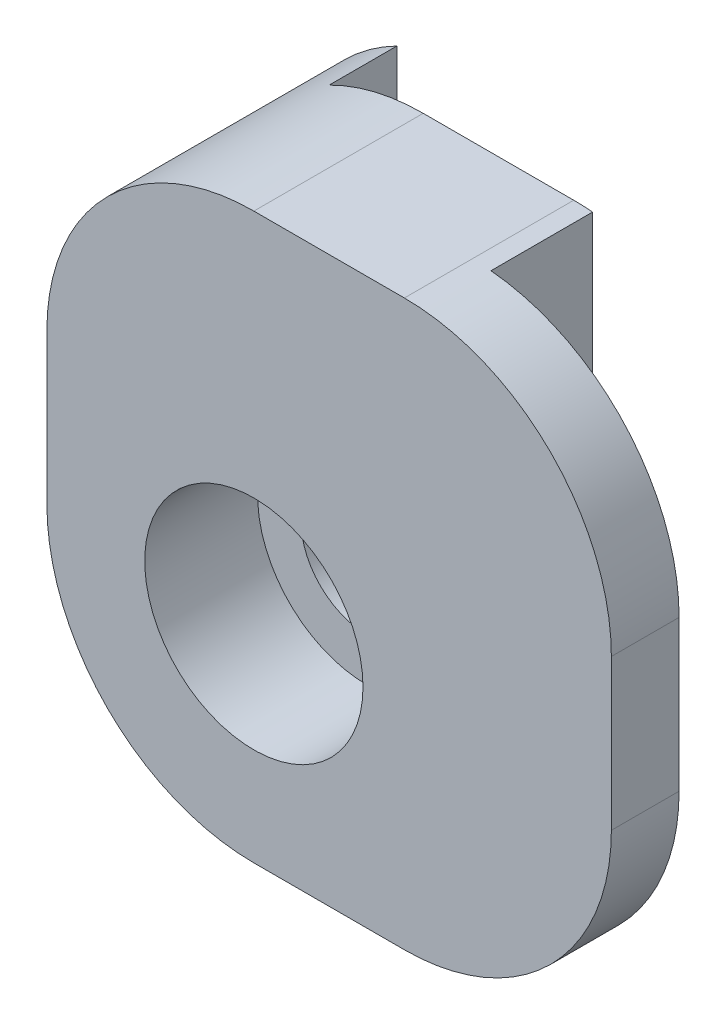
SolidWorks part; units mm, degrees
ref_plane "Plano frontal" through (0, 0, 0) normal (0, 0, 1) x (1, 0, 0)
ref_plane "Plano superior" through (0, 0, 0) normal (0, 1, 0) x (1, 0, 0)
ref_plane "Plano direito" through (0, 0, 0) normal (1, 0, 0) x (0, 0, -1)
sketch "Esboço3" plane through (0, 0, 0) normal (0, 0, 1) x (1, 0, 0)
  line L0 (0, 0) -> (-2.5, 2.5) construction
  line L1 (0, 0) -> (-7, 0)
  line L2 (0, 0) -> (0, 12)
  line L3 (0, 12) -> (-7, 12)
  line L4 (-7, 0) -> (-7, 12)
  circle A0 centre (-2.5, 2.5) radius 1.75
  dimension "D5" = 3.5
  dimension "D1" = 12
  dimension "D2" = 7
  dimension "D3" = 2.5
  dimension "D4" = 2.5
extrude "Ressalto-extrusão2" add sketch "Esboço3" along normal blind 2.7
sketch "Esboço4" plane through (0, 0, 2.7) normal (0, 0, 1) x (1, 0, 0)
  line L4 (0, 0) -> (0, 12)
  line L5 (0, 12) -> (-7, 12)
  line L6 (-7, 12) -> (-7, 0)
  line L7 (-7, 0) -> (0, 0)
  line L8 (0, 0) -> (0, 12)
  line L9 (0, 12) -> (-7, 12)
  line L10 (-7, 12) -> (-7, 0)
  line L11 (-7, 0) -> (0, 0)
  circle A0 centre (-2.5, 2.5) radius 1.75 construction
  circle A1 centre (-2.5, 2.5) radius 1.75
  dimension "D1" = 0
extrude "Ressalto-extrusão3" add sketch "Esboço4" along normal blind 2.1
sketch "Esboço5" plane through (-7, 0, 0) normal (-1, 0, 0) x (0, 0, 1)
  line L0 (4.8, 12) -> (4.8, 0) construction
  line L1 (4.8, 12) -> (4.8, 0)
  line L2 (2.7, 12) -> (2.7, 0)
  line L3 (4.8, 12) -> (2.7, 12)
  line L4 (2.7, 0) -> (4.8, 0)
  dimension "D1" = 2.1
extrude "Ressalto-extrusão4" add sketch "Esboço5" along normal blind 5
sketch "Esboço6" plane through (0, 0, 0) normal (0, -1, 0) x (1, 0, 0)
  line L6 (-7, 0) -> (0, 0)
  line L7 (0, 0) -> (0, 4.8)
  line L8 (0, 4.8) -> (-12, 4.8)
  line L9 (-12, 4.8) -> (-12, 2.7)
  line L10 (-12, 2.7) -> (-7, 2.7)
  line L11 (-7, 2.7) -> (-7, 0)
  line L12 (-7, 0) -> (0, 0)
  line L13 (0, 0) -> (0, 4.8)
  line L14 (0, 4.8) -> (-12, 4.8)
  line L15 (-12, 4.8) -> (-12, 2.7)
  line L16 (-12, 2.7) -> (-7, 2.7)
  line L17 (-7, 2.7) -> (-7, 0)
  dimension "D1" = 0
extrude "Ressalto-extrusão5" add sketch "Esboço6" along normal blind 3
sketch "Esboço7" plane through (0, 0, 0) normal (1, 0, 0) x (0, 0, -1)
  line L4 (0, -3) -> (0, 12)
  line L5 (0, 12) -> (-4.8, 12)
  line L6 (-4.8, 12) -> (-4.8, -3)
  line L7 (-4.8, -3) -> (0, -3)
  line L8 (0, -3) -> (0, 12)
  line L9 (0, 12) -> (-4.8, 12)
  line L10 (-4.8, 12) -> (-4.8, -3)
  line L11 (-4.8, -3) -> (0, -3)
  dimension "D1" = 0
extrude "Ressalto-extrusão6" add sketch "Esboço7" along normal blind 3
sketch "Esboço8" plane through (0, 0, 4.8) normal (0, 0, 1) x (1, 0, 0)
  circle A0 centre (-2.5, 2.5) radius 2.9
  dimension "D1" = 5.8
extrude "Corte-extrusão1" cut sketch "Esboço8" against normal blind 3
fillet "Filete1" radius 5.5 1 edges at (3, -3, 2.4)
sketch "Esboço10" plane through (0, 0, 0) normal (0, 0, -1) x (-1, 0, 0)
  line L0 (2.5, 2.5) -> (0, 0) construction
  line L1 (7, 12) -> (7, -3) construction
  line L2 (0, 0) -> (7, 0)
  line L3 (0, 0) -> (0, 14)
  line L4 (0, 14) -> (7, 14)
  line L5 (7, 0) -> (7, 14)
  line L6 (7, 12) -> (7, -3) construction
  line L7 (7, -3) -> (2.5, -3) construction
  line L8 (-3, 2.5) -> (-3, 12) construction
  line L9 (-3, 12) -> (7, 12) construction
  line L10 (7, -3) -> (2.5, -3)
  line L11 (-3, 2.5) -> (-3, 12)
  line L12 (-3, 12) -> (7, 12)
  line L13 (7, 12) -> (7, -3)
  arc A0 (-3, 2.5) -> (2.5, -3) centre (2.5, 2.5) ccw construction
  arc A1 (-3, 2.5) -> (2.5, -3) centre (2.5, 2.5) ccw
  line M10 (-3, 12) -> (-3, 2.5)
  arc M11 (-3, 2.5) -> (2.5, -3) centre (2.5, 2.5) ccw
  line M12 (2.5, -3) -> (7, -3)
  line M13 (7, -3) -> (7, 12)
  line M14 (7, 12) -> (-3, 12)
  dimension "D1" = 2.5
  dimension "D2" = 2.5
extrude "Ressalto-extrusão7" add sketch "Esboço10" along normal blind 1.5 contours L2 L3 M14 M10 M11 M12 M13
sketch "Esboço13" plane through (0, 0, 4.8) normal (0, 0, 1) x (1, 0, 0)
  line L0 (-2.5, -3) -> (-12, -3) construction
  line L1 (-12, -3) -> (-12, 12) construction
  line L6 (-12, -3) -> (-2.5, -3)
  line L7 (3, 2.5) -> (3, 12)
  line L8 (3, 12) -> (-12, 12)
  line L9 (-12, 12) -> (-12, -3)
  line L10 (-12, -3) -> (-6.5, -3)
  line L13 (-12, 2.5) -> (-12, -3)
  arc A0 (-12, 2.5) -> (-6.5, -3) centre (-6.5, 2.5) ccw
  arc A2 (-2.5, -3) -> (3, 2.5) centre (-2.5, 2.5) ccw
  dimension "D1" = 11
  dimension "D2" = 0
sketch "Esboço14" plane through (0, 0, 4.8) normal (0, 0, 1) x (1, 0, 0)
  line L4 (-12, -3) -> (-2.5, -3)
  line L5 (3, 2.5) -> (3, 12)
  line L6 (3, 12) -> (-12, 12)
  line L7 (-12, 12) -> (-12, -3)
  line L8 (-12, -3) -> (-2.5, -3)
  line L9 (3, 2.5) -> (3, 6.5)
  line L10 (-2.5, 12) -> (-6.5, 12)
  line L11 (-12, 6.5) -> (-12, -3)
  line L16 (3, 12) -> (3, 2.5) construction
  line L17 (-12, -3) -> (-12, 12) construction
  line L18 (3, 12) -> (-12, 12) construction
  line L19 (3, 12) -> (3, 2.5)
  line L20 (-12, -3) -> (-12, 12)
  line L21 (3, 12) -> (-12, 12)
  arc A0 (-12, 6.5) -> (-6.5, 12) centre (-6.5, 6.5) cw
  arc A1 (-2.5, 12) -> (3, 6.5) centre (-2.5, 6.5) cw
  arc A3 (-2.5, -3) -> (3, 2.5) centre (-2.5, 2.5) ccw
  arc A5 (-2.5, -3) -> (3, 2.5) centre (-2.5, 2.5) ccw
  line M15 (3, 2.5) -> (3, 12)
  line M16 (3, 12) -> (-12, 12)
  line M17 (-12, 12) -> (-12, -3)
  dimension "D2" = 5.5
  dimension "D1" = 0
extrude "Corte-extrusão4" cut sketch "Esboço14" against normal up to surface (6.3 mm away) contours A0 M17 M16 | A1 M16 M15 up to face at (-1.3373, 2.7658, -1.5)
extrude "Corte-extrusão5" cut sketch "Esboço13" against normal up to surface (6.3 mm away) contours A0 L10 L13 up to face at (-1.2386, 1.9547, -1.5)
sketch "Esboço15" plane through (0, 0, -1.5) normal (0, 0, -1) x (-1, 0, 0)
  line L5 (2.5, -3) -> (6.5, -3)
  line L6 (7, -2.9772) -> (7, 0)
  line L7 (7, 0) -> (0, 0)
  line L8 (0, 0) -> (0, 11.399)
  line L9 (-3, 6.5) -> (-3, 2.5)
  line L10 (2.5, -3) -> (6.5, -3)
  line L11 (7, -2.9772) -> (7, 0)
  line L12 (7, 0) -> (0, 0)
  line L13 (0, 0) -> (0, 11.399)
  line L14 (-3, 6.5) -> (-3, 2.5)
  arc A3 (6.5, -3) -> (7, -2.9772) centre (6.5, 2.5) ccw
  arc A4 (0, 11.399) -> (-3, 6.5) centre (2.5, 6.5) ccw
  arc A5 (-3, 2.5) -> (2.5, -3) centre (2.5, 2.5) ccw
  arc A6 (6.5, -3) -> (7, -2.9772) centre (6.5, 2.5) ccw
  arc A7 (0, 11.399) -> (-3, 6.5) centre (2.5, 6.5) ccw
  arc A8 (-3, 2.5) -> (2.5, -3) centre (2.5, 2.5) ccw
  dimension "D1" = 0
extrude "Ressalto-extrusão8" add sketch "Esboço15" along normal blind 0.3
ref_plane "Plano1" through (4, 0, 0) normal (1, 0, 0) x (0, 0, -1)
mirror "Espelhar3" about plane through (4, 0, 0) normal (1, 0, 0) of bodies 115
delete or keep bodies "Corpo-Excluir/Manter 1" type delete bodies bodies 115
sketch "Esboço16" plane through (0, 0, 4.8) normal (0, 0, 1) x (1, 0, 0)
  line L4 (20, 2.5) -> (20, 6.5)
  line L5 (14.5, 12) -> (10.5, 12)
  line L6 (5, 6.5) -> (5, 2.5)
  line L7 (10.5, -3) -> (14.5, -3)
  line L8 (20, 2.5) -> (20, 6.5)
  line L9 (14.5, 12) -> (10.5, 12)
  line L10 (5, 6.5) -> (5, 2.5)
  line L11 (10.5, -3) -> (14.5, -3)
  arc A4 (20, 6.5) -> (14.5, 12) centre (14.5, 6.5) ccw
  arc A5 (10.5, 12) -> (5, 6.5) centre (10.5, 6.5) ccw
  arc A6 (5, 2.5) -> (10.5, -3) centre (10.5, 2.5) ccw
  arc A7 (14.5, -3) -> (20, 2.5) centre (14.5, 2.5) ccw
  arc A8 (20, 6.5) -> (14.5, 12) centre (14.5, 6.5) ccw
  arc A9 (10.5, 12) -> (5, 6.5) centre (10.5, 6.5) ccw
  arc A10 (5, 2.5) -> (10.5, -3) centre (10.5, 2.5) ccw
  arc A11 (14.5, -3) -> (20, 2.5) centre (14.5, 2.5) ccw
  dimension "D1" = 0
extrude "Corte-extrusão6" cut sketch "Esboço16" against normal blind 0.3
sketch "Esboço17" plane through (0, 0, 1.8) normal (0, 0, 1) x (1, 0, 0)
  circle A1 centre (10.5, 2.5) radius 2.9
  circle A2 centre (10.5, 2.5) radius 2.9
  dimension "D1" = 0
extrude "Corte-extrusão7" cut sketch "Esboço17" against normal blind 0.3
